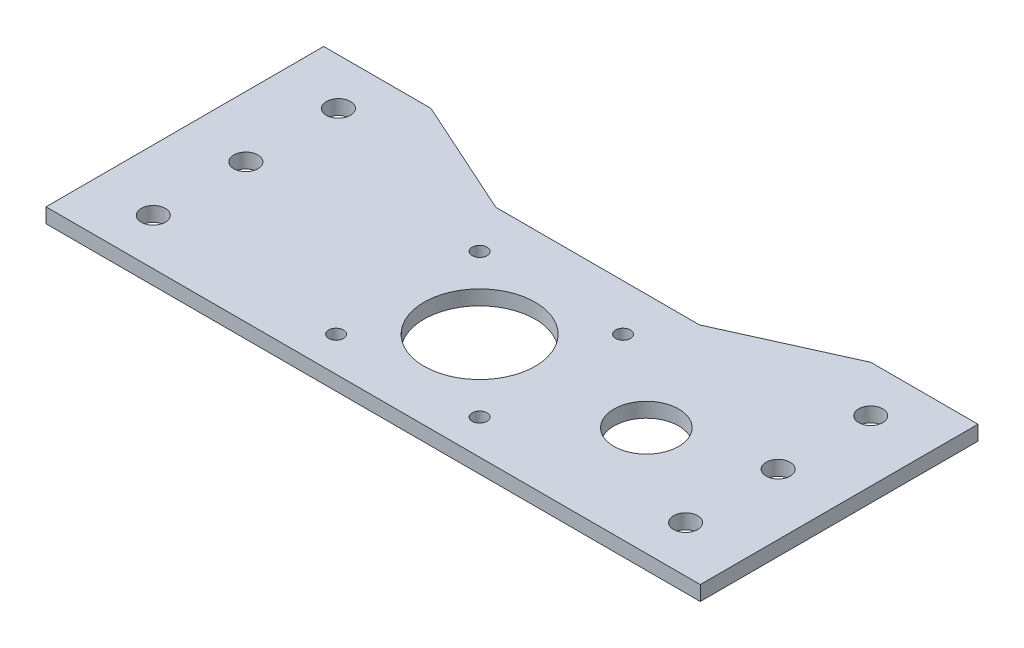
SolidWorks part; units mm, degrees
material "6061-T6 (SS)"
ref_plane "Front Plane" through (0, 0, 0) normal (0, 0, 1) x (1, 0, 0)
ref_plane "Top Plane" through (0, 0, 0) normal (0, 1, 0) x (1, 0, 0)
ref_plane "Right Plane" through (0, 0, 0) normal (1, 0, 0) x (0, 0, -1)
sketch "Sketch2" plane through (0, 0, 0) normal (0, 1, 0) x (1, 0, 0)
  line L0 (0, 0) -> (0, 60) construction
  line L1 (70.675, 0) -> (-70.675, 0)
  line L2 (-70.675, 0) -> (-70.675, 60)
  line L3 (-70.675, 60) -> (-47.5, 60)
  line L4 (-47.5, 60) -> (-22, 48.5)
  line L5 (-22, 48.5) -> (22, 48.5)
  line L6 (-57.5, 60) -> (-57.5, 0) construction
  line L7 (-70.675, 30) -> (0, 30) construction
  line L8 (70.675, 0) -> (70.675, 60)
  line L9 (70.675, 60) -> (47.5, 60)
  line L10 (47.5, 60) -> (22, 48.5)
  line L11 (-67.5, 60) -> (-67.5, 0) construction
  line L12 (67.5, 60) -> (67.5, 0) construction
  line L13 (15.5, 7.5) -> (-15.5, 7.5) construction
  line L14 (15.5, 7.5) -> (15.5, 38.5) construction
  line L15 (15.5, 38.5) -> (-15.5, 38.5) construction
  line L16 (-15.5, 7.5) -> (-15.5, 38.5) construction
  line L17 (15.5, 7.5) -> (-15.5, 38.5) construction
  line L18 (15.5, 38.5) -> (-15.5, 7.5) construction
  circle A0 centre (-57.5, 30) radius 2.6
  circle A1 centre (-57.5, 50) radius 2.6
  circle A2 centre (-57.5, 10) radius 2.6
  circle A3 centre (0, 23) radius 12
  circle A4 centre (-15.5, 38.5) radius 1.6
  circle A5 centre (15.5, 38.5) radius 1.6
  circle A6 centre (15.5, 7.5) radius 1.6
  circle A7 centre (-15.5, 7.5) radius 1.6
  circle A8 centre (57.5, 10) radius 2.6
  circle A9 centre (57.5, 30) radius 2.6
  circle A10 centre (57.5, 50) radius 2.6
  circle A11 centre (35.5, 23.525) radius 7
  point P32 (0, 23)
  point P39 (0, 48.5)
  dimension "D7" = 5.2
  dimension "D8" = 10
  dimension "D9" = 24
  dimension "D11" = 3.2
  dimension "D16" = 14
  dimension "D17" = 23.525
  dimension "D18" = 35.5
  dimension "D2" = 60
  dimension "D3" = 44
  dimension "D4" = 3.175
  dimension "D5" = 48.5
  dimension "D6" = 10
  dimension "D10" = 23
  dimension "D12" = 31
  dimension "D13" = 135
  dimension "D15" = 10
  dimension "D14" = 4
extrude "Boss-Extrude1" add sketch "Sketch2" along normal blind 3.175
